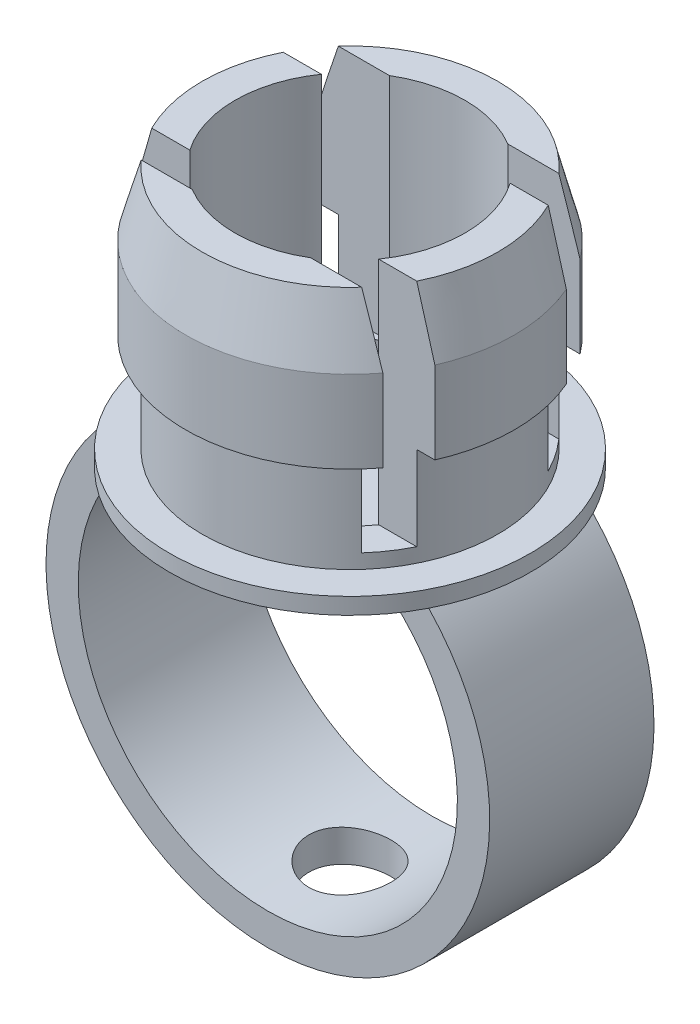
SolidWorks part; units mm, degrees
ref_plane "Alzado" through (0, 0, 0) normal (0, 0, 1) x (1, 0, 0)
ref_plane "Planta" through (0, 0, 0) normal (0, 1, 0) x (1, 0, 0)
ref_plane "Vista lateral" through (0, 0, 0) normal (1, 0, 0) x (0, 0, -1)
sketch "Croquis1" plane through (0, 0, 0) normal (0, 0, 1) x (1, 0, 0)
  line L1 (-89.7781, -14.638) -> (-78.7823, -14.638)
  line L2 (-78.7823, -14.638) -> (-78.7823, -13.638)
  line L3 (-87.7823, -13.638) -> (-87.7823, -7.638)
  line L4 (-87.7823, -7.638) -> (-88.7823, -7.638)
  line L5 (-88.7823, -7.638) -> (-88.7823, -2.638)
  line L6 (-88.7823, -2.638) -> (-87.7823, 1.236)
  line L7 (-87.7823, 1.236) -> (-85.7823, 1.236)
  line L8 (-85.7823, 1.236) -> (-85.7823, -13.638)
  line L9 (-85.7823, -13.638) -> (-78.7823, -13.638)
  line L11 (-89.7781, -13.638) -> (-89.7781, -14.638)
  line L14 (-87.7823, -13.638) -> (-89.7781, -13.638)
  dimension "D1" = 15.874
revolve "Revolución1" add sketch "Croquis1" angle 360 about L2
sketch "Croquis2" plane through (0, 1.236, 0) normal (0, 1, 0) x (1, 0, 0)
  line L0 (-87.7823, 0) -> (-69.7823, 0) construction
  line L6 (-91.7823, -4) -> (-65.7823, -4)
  line L7 (-91.7823, -4) -> (-91.7823, -6)
  line L8 (-91.7823, -6) -> (-65.7823, -6)
  line L9 (-65.7823, -4) -> (-65.7823, -6)
  line L10 (-91.7823, 4) -> (-65.7823, 4)
  line L11 (-91.7823, 4) -> (-91.7823, 6)
  line L12 (-91.7823, 6) -> (-65.7823, 6)
  line L13 (-65.7823, 4) -> (-65.7823, 6)
  circle A1 centre (-78.7823, 0) radius 9 construction
  dimension "D1" = 2
  dimension "D2" = 2
  dimension "D3" = 4
  dimension "D4" = 4
extrude "Cortar-Extruir1" cut sketch "Croquis2" against normal blind 14
sketch "Croquis3" plane through (0, -14.638, 0) normal (0, -1, 0) x (1, 0, 0)
  line L0 (-78.7823, 0) -> (-78.7823, 5) construction
  line L1 (-78.7823, 5) -> (-92.2823, 5) construction
  line L2 (-92.2823, 5) -> (-92.2823, -5) construction
  line L4 (-92.2823, 5) -> (-65.2823, 5)
  line L5 (-92.2823, 5) -> (-92.2823, -5)
  line L6 (-92.2823, -5) -> (-65.2823, -5)
  line L7 (-65.2823, 5) -> (-65.2823, -5)
  dimension "D1" = 13.5
  dimension "D2" = 5
  dimension "D3" = 10
  dimension "D4" = 27
extrude "Saliente-Extruir1" add sketch "Croquis3" along normal blind 24
sketch "Croquis4" plane through (0, 0, -5) normal (0, 0, -1) x (-1, 0, 0)
  line L0 (88.5755, -14.638) -> (92.2823, -14.638)
  line L1 (92.2823, -14.638) -> (92.2823, -38.638)
  line L2 (92.2823, -38.638) -> (65.2823, -38.638)
  line L3 (65.2823, -38.638) -> (65.2823, -14.638)
  line L4 (65.2823, -14.638) -> (68.989, -14.638)
  line L5 (88.5755, -14.638) -> (85.5755, -14.638)
  line L6 (68.989, -14.638) -> (71.989, -14.638)
  arc A0 (88.5755, -14.638) -> (68.989, -14.638) centre (78.7823, -23.93) cw
  arc A1 (85.5755, -14.638) -> (71.989, -14.638) centre (78.7823, -23.9622) cw
  line M1 (92.2823, -14.638) -> (88.5755, -14.638)
  line M2 (88.5755, -14.638) -> (68.989, -14.638)
  line M3 (68.989, -14.638) -> (65.2823, -14.638)
  line M4 (65.2823, -14.638) -> (65.2823, -38.638)
  line M5 (65.2823, -38.638) -> (92.2823, -38.638)
  line M6 (92.2823, -38.638) -> (92.2823, -14.638)
  dimension "D1" = 3
  dimension "D2" = 3
extrude "Cortar-Extruir2" cut sketch "Croquis4" against normal up to vertex (10 mm away) contours A0 L3 M6 M5 | A0 L1 M1 | A0 M4 M3 | A1 M2
sketch "Croquis5" plane through (0, -13.638, 0) normal (0, 1, 0) x (1, 0, 0)
  circle A0 centre (-78.7823, 0) radius 1.5
extrude "Cortar-Extruir3" cut sketch "Croquis5" against normal blind 24
sketch "Croquis6" plane through (0, -14.638, 0) normal (0, -1, 0) x (1, 0, 0)
  circle A0 centre (-78.7823, 0) radius 2.5
extrude "Cortar-Extruir4" cut sketch "Croquis6" along normal blind 24
